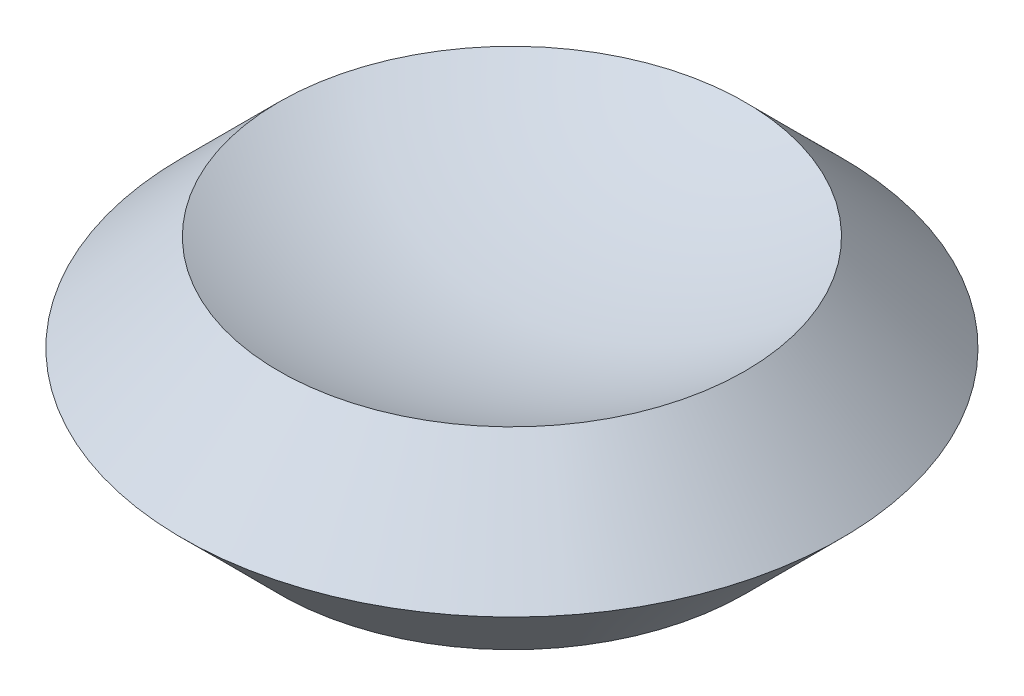
SolidWorks part; units mm, degrees
ref_plane "Front Plane" through (0, 0, 0) normal (0, 0, 1) x (1, 0, 0)
ref_plane "Top Plane" through (0, 0, 0) normal (0, 1, 0) x (1, 0, 0)
ref_plane "Right Plane" through (0, 0, 0) normal (1, 0, 0) x (0, 0, -1)
sketch "Electromagnetic Base Sketch" plane through (0, 0, 0) normal (0, 0, 1) x (1, 0, 0)
  line L4 (0, 21.33) -> (0, 0)
  line L5 (-36.23, 0) -> (0, 0)
  line L7 (-36.23, 30) -> (-51.23, 15)
  line L8 (-51.23, 15) -> (-36.23, 0)
  line L9 (-84.5642, 15) -> (12.1042, 15) construction
  arc A1 (-36.23, 30) -> (0, 21.33) centre (0, 101.3636) ccw
  point P10 (-36.23, 15)
  dimension "D1" = 36.23
  dimension "D2" = 30
  dimension "D3" = 21.33
  dimension "D4" = 15
revolve "Electromagnetic Base Body" add sketch "Electromagnetic Base Sketch" angle 360 about L4
